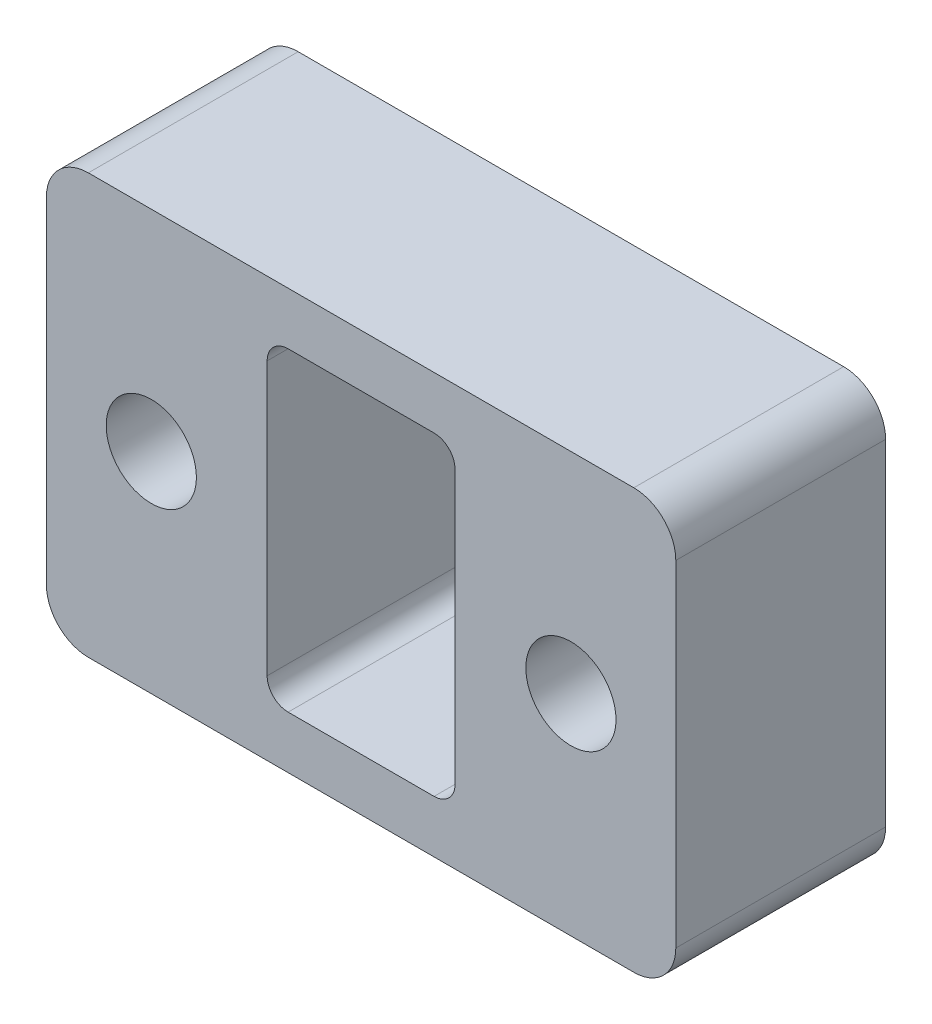
SolidWorks part; units mm, degrees
ref_plane "前视基准面" through (0, 0, 0) normal (0, 0, 1) x (1, 0, 0)
ref_plane "上视基准面" through (0, 0, 0) normal (0, 1, 0) x (1, 0, 0)
ref_plane "右视基准面" through (0, 0, 0) normal (1, 0, 0) x (0, 0, -1)
other "Configuration Table"
sketch "草图1" plane through (0, 0, 0) normal (0, 0, 1) x (1, 0, 0)
  line L0 (-10, 0) -> (10, 0) construction
  line L1 (-15, -10) -> (15, -10)
  line L2 (-15, -10) -> (-15, 10)
  line L3 (-15, 10) -> (15, 10)
  line L4 (15, -10) -> (15, 10)
  line L5 (-15, -10) -> (15, 10) construction
  line L6 (-15, 10) -> (15, -10) construction
  line L22 (-4.4782, -7.5) -> (4.4782, -7.5)
  line L23 (-4.4782, -7.5) -> (-4.4782, 7.5)
  line L24 (-4.4782, 7.5) -> (4.4782, 7.5)
  line L25 (4.4782, -7.5) -> (4.4782, 7.5)
  line L26 (-4.4782, -7.5) -> (4.4782, 7.5) construction
  line L27 (-4.4782, 7.5) -> (4.4782, -7.5) construction
  circle A0 centre (-10, 0) radius 2.15
  circle A1 centre (10, 0) radius 2.15
  point P0 (0, 0)
  point P6 (0, 0)
  point P9 (0, 0)
  dimension "D5" = 2.5
  dimension "D3" = 4.3
  dimension "D1" = 20
  dimension "D2" = 20
  dimension "D4" = 5
  dimension "D6" = 8.9563
extrude "凸台-拉伸1" add sketch "草图1" along normal blind 10
fillet "圆角1" radius 1 4 edges at (4.4782, 7.5, 5) (-4.4782, -7.5, 5) (4.4782, -7.5, 5) (-4.4782, 7.5, 5)
fillet "圆角2" radius 2 4 edges at (15, -10, 5) (-15, -10, 5) (-15, 10, 5) (15, 10, 5)
